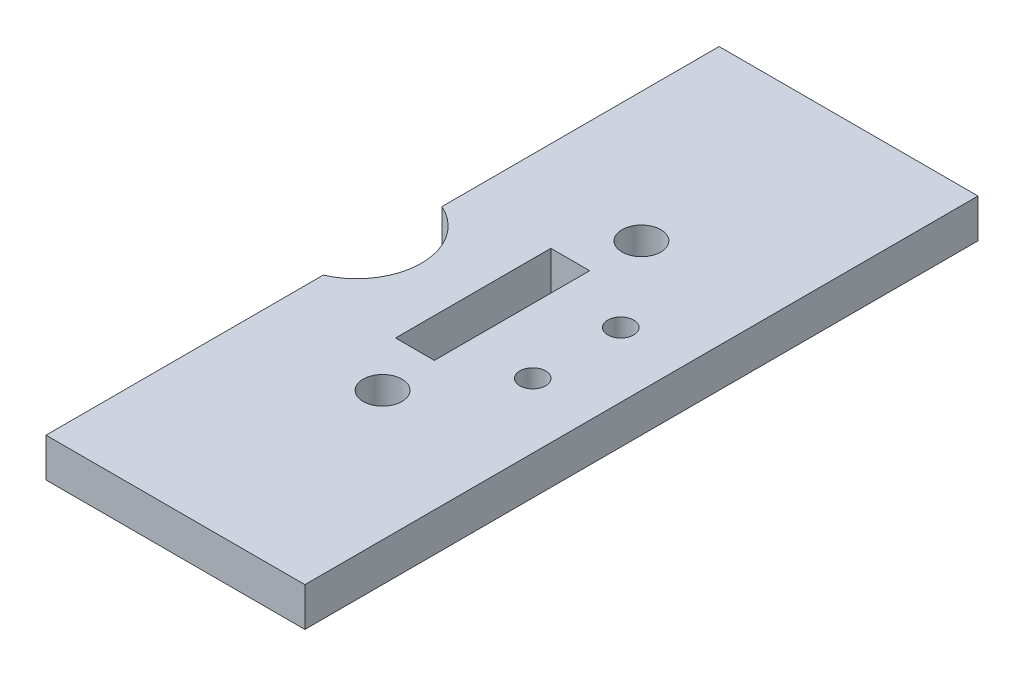
SolidWorks part; units mm, degrees
material "Balsa"
ref_plane "Plan de face" through (0, 0, 0) normal (0, 0, 1) x (1, 0, 0)
ref_plane "Plan de dessus" through (0, 0, 0) normal (0, 1, 0) x (1, 0, 0)
ref_plane "Plan de droite" through (0, 0, 0) normal (1, 0, 0) x (0, 0, -1)
sketch "Esquisse1" plane through (0, 0, 0) normal (0, 1, 0) x (1, 0, 0)
  line L1 (-21.986, -5.9334) -> (-1.986, -5.9334)
  line L2 (-21.986, -5.9334) -> (-21.986, -57.9334)
  line L3 (-21.986, -57.9334) -> (-1.986, -57.9334)
  line L4 (-1.986, -5.9334) -> (-1.986, -57.9334)
  dimension "D1" = 52
  dimension "D2" = 20
extrude "Boss.-Extru.1" add sketch "Esquisse1" along normal blind 3
sketch "Esquisse2" plane through (0, 3, 0) normal (0, 1, 0) x (1, 0, 0)
  line L0 (-1.986, -57.9334) -> (-1.986, -5.9334) construction
  line L3 (-21.986, -57.9334) -> (-1.986, -57.9334) construction
  circle A0 centre (-11.986, -41.9334) radius 1.5
  circle A1 centre (-11.986, -21.9334) radius 1.5
  dimension "D1" = 3
  dimension "D2" = 3
  dimension "D3" = 10
  dimension "D4" = 10
  dimension "D5" = 20
  dimension "D6" = 16
extrude "Enlèv. mat.-Extru.1" cut sketch "Esquisse2" against normal blind 3
sketch "Esquisse3" plane through (0, 3, 0) normal (0, 1, 0) x (1, 0, 0)
  line L1 (-21.986, -57.9334) -> (-1.986, -57.9334) construction
  line L2 (-21.986, -5.9334) -> (-21.986, -57.9334) construction
  circle A0 centre (-23.986, -31.9334) radius 5
  dimension "D1" = 10
  dimension "D2" = 2
  dimension "D3" = 26
extrude "Enlèv. mat.-Extru.2" cut sketch "Esquisse3" against normal blind 3
sketch "Esquisse4" plane through (0, 3, 0) normal (0, 1, 0) x (1, 0, 0)
  line L0 (-1.986, -57.9334) -> (-1.986, -5.9334) construction
  line L1 (-11.986, -37.931) -> (-14.986, -37.931)
  line L2 (-11.986, -37.931) -> (-11.986, -25.931)
  line L3 (-11.986, -25.931) -> (-14.986, -25.931)
  line L4 (-14.986, -37.931) -> (-14.986, -25.931)
  dimension "D1" = 10
  dimension "D2" = 3
  dimension "D3" = 12
  dimension "D4" = 1.415
  dimension "D5" = 1.4198
extrude "Enlèv. mat.-Extru.3" cut sketch "Esquisse4" against normal blind 10
sketch "Esquisse5" plane through (0, 3, 0) normal (0, 1, 0) x (1, 0, 0)
  circle A0 centre (-6.986, -35.331) radius 1
  circle A1 centre (-6.986, -28.531) radius 1
  dimension "D1" = 2
  dimension "D2" = 2
extrude "Enlèv. mat.-Extru.5" cut sketch "Esquisse5" against normal blind 10
